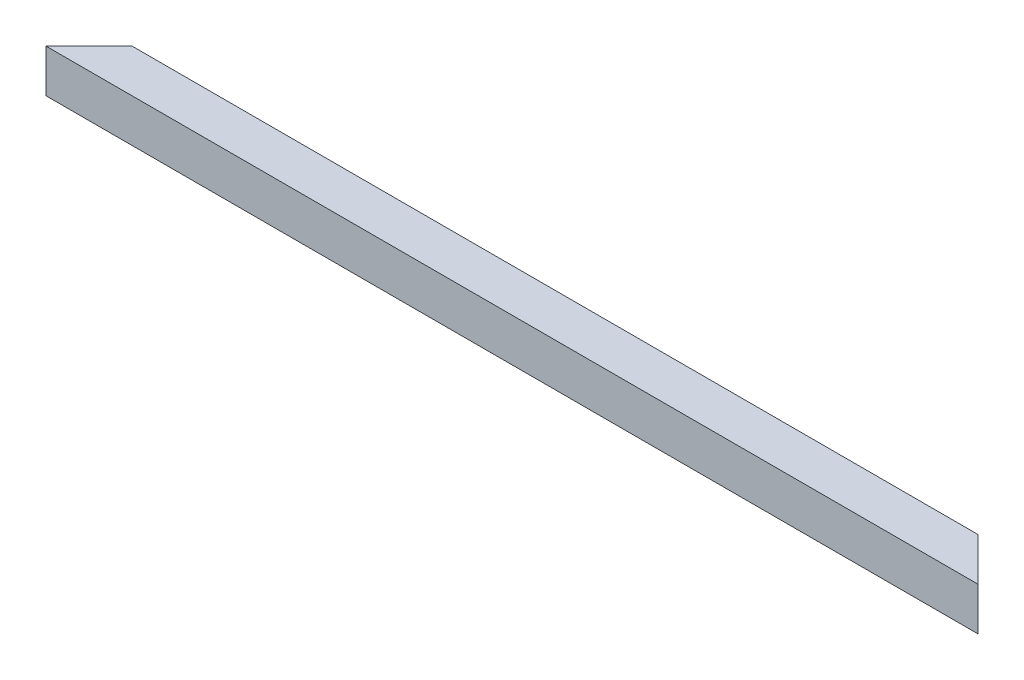
SolidWorks part; units mm, degrees
ref_plane "Alzado" through (0, 0, 0) normal (0, 0, 1) x (1, 0, 0)
ref_plane "Planta" through (0, 0, 0) normal (0, 1, 0) x (1, 0, 0)
ref_plane "Vista lateral" through (0, 0, 0) normal (1, 0, 0) x (0, 0, -1)
sketch "Sketch1" plane through (0, 0, 0) normal (0, 1, 0) x (1, 0, 0)
  line L0 (0, 0) -> (550, 0)
  line L1 (550, 0) -> (550, 25.4)
  line L2 (550, 25.4) -> (0, 25.4)
  line L3 (0, 25.4) -> (0, 0)
  dimension "D1" = 550
  dimension "D2" = 25.4
extrude "Boss-Extrude1" add sketch "Sketch1" along normal blind 25.4
sketch "Sketch2" plane through (550, 0, 0) normal (1, 0, 0) x (0, 0, -1)
  line L0 (1.2, 1.2) -> (24.2, 1.2)
  line L1 (24.2, 1.2) -> (24.2, 24.2)
  line L2 (24.2, 24.2) -> (1.2, 24.2)
  line L3 (1.2, 24.2) -> (1.2, 1.2)
  line L4 (0, 0) -> (25.4, 0) construction
  line L5 (0, 25.4) -> (25.4, 25.4) construction
  line L6 (25.4, 25.4) -> (25.4, 0) construction
  line L7 (0, 25.4) -> (0, 0) construction
  dimension "D1" = 1.2
  dimension "D2" = 1.2
  dimension "D3" = 1.2
  dimension "D4" = 1.2
extrude "Cut-Extrude1" cut sketch "Sketch2" against normal blind 550
sketch "Sketch3" plane through (0, 25.4, 0) normal (0, 1, 0) x (1, 0, 0)
  line L0 (0, 0) -> (25.4, 25.4)
  line L1 (550, 25.4) -> (0, 25.4) construction
  line L2 (550, 0) -> (524.6, 25.4)
  line L3 (25.4, 25.4) -> (0, 25.4)
  line L4 (0, 25.4) -> (0, 0)
  line L5 (524.6, 25.4) -> (550, 25.4)
  line L6 (550, 25.4) -> (550, 0)
  dimension "D1" = 25.4
  dimension "D2" = 25.4
extrude "Cut-Extrude2" cut sketch "Sketch3" against normal blind 25.4
